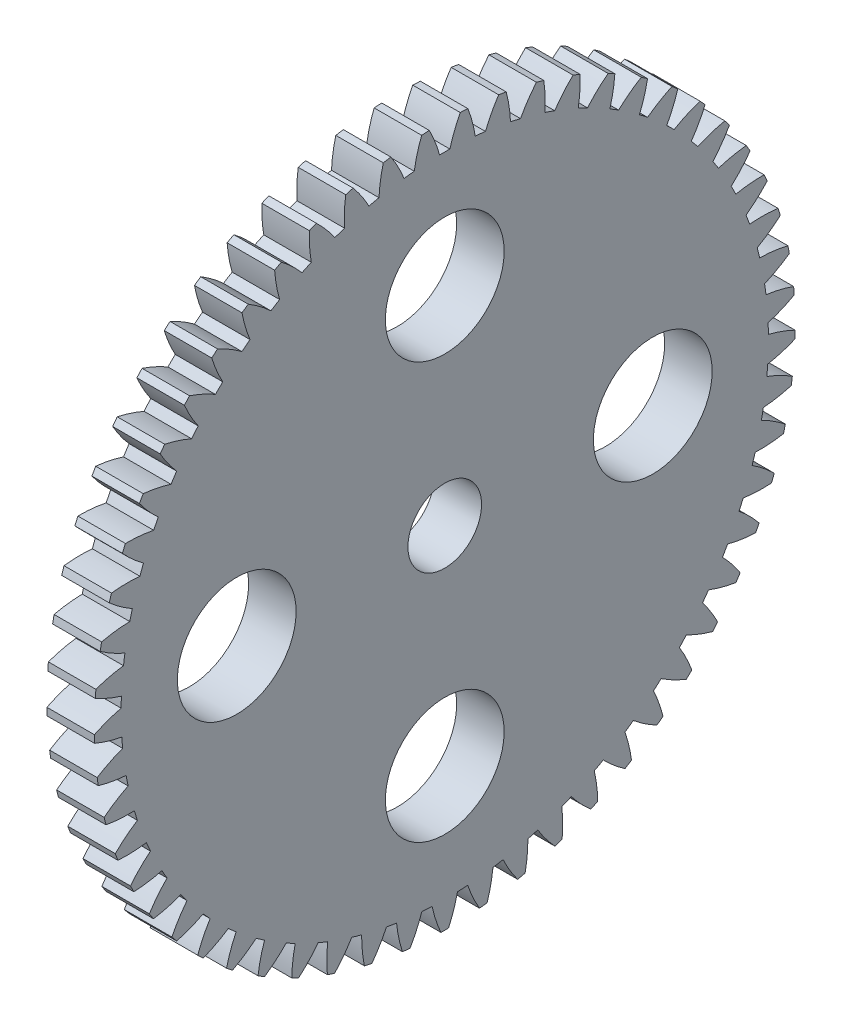
SolidWorks part; units mm, degrees
ref_plane "Plane1" through (0, 0, 0) normal (0, 0, 1) x (1, 0, 0)
ref_plane "Plane2" through (0, 0, 0) normal (0, 1, 0) x (1, 0, 0)
ref_plane "Plane3" through (0, 0, 0) normal (1, 0, 0) x (0, 0, -1)
sketch "HoldingSke" plane through (0, 0, 0) normal (0, 1, 0) x (1, 0, 0)
  line L0 (0, 0) -> (0.5446, -0.8387)
  line L1 (-15, 0) -> (100, 0) construction
  line L2 (0, 0) -> (-2.1039, 2.3779)
  line L3 (0, 0) -> (-11.863, 4.5341)
  line L4 (0, 0) -> (4.7035, 7.2428)
  line L5 (0, 0) -> (-46.8476, -17.4728)
  line L6 (0, 0) -> (-3.3159, -2.2372)
  line L7 (-2.1039, 2.3779) -> (8.6586, 51.2059)
  line L8 (-76.2, 54.61) -> (-75.7, 54.61)
  line L9 (-71.009, 38.7566) -> (-53.1078, 45.2721)
  line L10 (-76.2, 71.12) -> (104.1128, 71.12)
  line L11 (0, 0) -> (-4, 0)
  line L12 (-76.2, 101.6) -> (-76.162, 101.6)
  line L13 (24.9733, 27.94) -> (52.9518, 28.4284)
  line L14 (24.9733, 27.94) -> (24.9743, 27.94)
  line L15 (24.9733, 27.94) -> (100.4006, 29.5858)
  line L16 (-63.627, -1) -> (-12.827, -1)
  circle A0 centre (0, 0) radius 1.5
  circle A1 centre (0, 0) radius 27.249
  circle A2 centre (0, 0) radius 37.5
  circle A3 centre (0, 0) radius 1.5
  dimension "MHD" = 54.498
  dimension "Hub_dia" = 75
  dimension "Bore" = 3
  dimension "MBD" = 3
  dimension "Num_teeth" = 57
  dimension "Pitch" = 1
  dimension "Overall_len" = 50
  dimension "Show_teeth" = 57
  dimension "Thickness" = 4
  dimension "OAL" = 50.0001
  dimension "T_dim" = 0.5
  dimension "Ap" = 20
  dimension "H" = 19.05
  dimension "Pitch_radius" = 180.3128
  dimension "Width" = 4
  dimension "Backlash" = 0.038
  dimension "Addendum_fac" = 1
  dimension "Dedendum_fac" = 1.25
  dimension "Clearance_fac" = 0.25
  dimension "Dedendum_add" = 0.001
  dimension "Module" = 1
sketch "BasProSke" plane through (0, 0, 0) normal (0, 1, 0) x (1, 0, 0)
  line L0 (-10, 0) -> (60, 0) construction
  line L1 (0, 0) -> (0, 29.5)
  line L2 (0, 0) -> (4, 0)
  line L3 (4, 0) -> (4, 29.5)
  line L4 (4, 29.5) -> (0, 29.5)
  dimension "Thickness" = 4
  dimension "Diameter" = 59
revolve "Base-Revolve" add sketch "BasProSke" angle 360 about L0
sketch "TooCutSke" plane through (0, 0, 0) normal (1, 0, 0) x (0, 0, -1)
  line L1 (0, 0) -> (0, 107) construction
  line L2 (0, 0) -> (-0.8518, 28.4873) construction
  line L3 (0, 0) -> (-3.139, 56.8953) construction
  line L4 (-0.8518, 28.4873) -> (-1.5695, 28.4477) construction
  arc A0 (0.4321, 27.2456) -> (-0.4321, 27.2456) centre (0, 0) ccw
  arc A1 (1.3171, 29.496) -> (-1.3171, 29.496) centre (0, 0) ccw
  circle A2 centre (0, 0) radius 28.5 construction
  circle A3 centre (0, 0) radius 26.7812 construction
  arc A4 (-0.4321, 27.2456) -> (-1.3171, 29.496) centre (-11.424, 24.2225) ccw
  arc A5 (1.3171, 29.496) -> (0.4321, 27.2456) centre (11.424, 24.2225) ccw
  dimension "Root_dia" = 54.498
  dimension "Overcut_dia" = 59.0508
  dimension "Pitch_dia" = 57
  dimension "Base_dia" = 53.5625
  dimension "Flank_rad" = 11.4
  dimension "Half_ang" = 3.158
  dimension "Half_CT" = 0.7188
extrude "ToothCut" cut sketch "TooCutSke" along normal through all
fillet "Breaks" [suppressed] radius 0.02
fillet "RootFillets" [suppressed] radius 0.251
pattern_circular "TeethCuts" count 57 every 6.316 about axis through (-10, 0, 0) along (1, 0, 0) of "ToothCut", "RootFillets", "Breaks"
sketch "HubNeaOneSke" plane through (0, 0, 0) normal (-1, 0, 0) x (0, 0, 1)
  circle A0 centre (0, 0) radius 27.249
  dimension "Diameter" = 54.498
extrude "HubNearOne" [suppressed] add sketch "HubNeaOneSke" along normal blind 46.0001
sketch "HubNeaBotSke" plane through (0, 0, 0) normal (-1, 0, 0) x (0, 0, 1)
  circle A0 centre (0, 0) radius 27.249
  dimension "Diameter" = 54.498
extrude "HubNearBoth" [suppressed] add sketch "HubNeaBotSke" along normal blind 23
ref_plane "FarPln" through (4, 0, 0) normal (1, 0, 0) x (0, 0, -1)
sketch "HubFarSke" plane through (4, 0, 0) normal (1, 0, 0) x (0, 0, -1)
  circle A0 centre (0, 0) radius 27.249
  dimension "Diameter" = 54.498
extrude "HubFar" [suppressed] add sketch "HubFarSke" along normal blind 23
sketch "BorSke" plane through (0, 0, 0) normal (1, 0, 0) x (0, 0, -1)
  circle A0 centre (0, 0) radius 3.1
  dimension "Diameter" = 6.2
extrude "Bore" cut sketch "BorSke" along normal mid plane 100.0001
sketch "KeySke" plane through (0, 0, 0) normal (1, 0, 0) x (0, 0, -1)
  line L0 (-0.6, 0) -> (-0.6, 2)
  line L1 (-0.6, 2) -> (0.6, 2)
  line L2 (0.6, 2) -> (0.6, 0)
  line L3 (0, 0) -> (0, 34) construction
  line L4 (-0.6, 0) -> (0.6, 0)
  dimension "Offset" = 2
  dimension "Width" = 1.2
extrude "Keyway" [suppressed] cut sketch "KeySke" along normal mid plane 100.0001
pattern_circular "Keyway2" [suppressed] count 2 every 90 about axis through (-10, 0, 0) along (1, 0, 0)
sketch "Sketch1" plane through (4, 0, 0) normal (1, 0, 0) x (0, 0, -1)
  circle A0 centre (0, -17.5134) radius 5
  circle A1 centre (-17.5134, 0) radius 5
  circle A2 centre (0, 17.5134) radius 5
  circle A3 centre (17.5134, 0) radius 5
  point P11 (0, 0)
  dimension "D2" = 10
  dimension "D1" = 4
extrude "Cut-Extrude1" cut sketch "Sketch1" against normal blind 10
equation "' \"Module@HoldingSke\" = 6.35"
equation "' \"Num_teeth@HoldingSke\" = 12"
equation "' \"Ap@HoldingSke\" =  20"
equation "' \"Ap@HoldingSke\" = 20"
equation "' \"Width@HoldingSke\" = 0.5 * 25.4"
equation "' \"Hub_dia@HoldingSke\"= 1 * 25.4"
equation "' \"Hub_dia@HoldingSke\" = 1 * 25.4"
equation "' \"Overall_len@HoldingSke\" = 1.0 * 25.4"
equation "' \"Bore@HoldingSke\" = 0.75 * 25.4"
equation "' \"T_dim@HoldingSke\" = 0.1 * 25.4"
equation "' \"Width@KeySke\" = 0.25 * 25.4"
equation "' \"Show_teeth@HoldingSke\" = 13"
equation "' \"Backlash@HoldingSke\" = 0.009 * 25.4"
equation "' \"Addendum_fac@HoldingSke\" = 1.0"
equation "' \"Dedendum_fac@HoldingSke\" = 1.25"
equation "' \"Dedendum_add@HoldingSke\" = 0.00005 * 25.4"
equation "' \"Clearance_fac@HoldingSke\" = 0.25"
equation "\"Pitch@HoldingSke\" = 1 / \"Module@HoldingSke\""
equation "\"Overcut_dia@TooCutSke\" = (\"Num_teeth@HoldingSke\" + 2 * \"Addendum_fac@HoldingSke\") / \"Pitch@HoldingSke\" + 0.002 * 25.4"
equation "\"Pitch_dia@TooCutSke\" = \"Num_teeth@HoldingSke\" / \"Pitch@HoldingSke\""
equation "\"Base_dia@TooCutSke\" = \"Num_teeth@HoldingSke\" / \"Pitch@HoldingSke\" * cos((\"Ap@HoldingSke\"  * 3.14159265 / 180))"
equation "\"Root_dia@TooCutSke\" = (\"Num_teeth@HoldingSke\" + 2) / \"Pitch@HoldingSke\" - 2 * (\"Addendum_fac@HoldingSke\" + \"Dedendum_fac@HoldingSke\") / \"Pitch@HoldingSke\" - \"Dedendum_add@HoldingSke\" * 2"
equation "\"Half_ang@TooCutSke\" = 180 / \"Num_teeth@HoldingSke\""
equation "\"Half_CT@TooCutSke\" = \"Num_teeth@HoldingSke\" / \"Pitch@HoldingSke\" * sin((3.14159265 / 2 / \"Num_teeth@HoldingSke\")) / 2 - 7 * \"Backlash@HoldingSke\" / 4"
equation "\"Flank_rad@TooCutSke\" = \"Num_teeth@HoldingSke\" / \"Pitch@HoldingSke\" / 5"
equation "\"Radius@RootFillets\" = \"Clearance_fac@HoldingSke\" / \"Pitch@HoldingSke\" + \"Dedendum_add@HoldingSke\""
equation "\"Break_rad@Breaks\" = 0.02 / \"Pitch@HoldingSke\""
equation "\"Thickness@HoldingSke\" = \"Width@HoldingSke\""
equation "\"OAL@HoldingSke\" = \"Thickness@HoldingSke\""
equation "\"MHD@HoldingSke\" = (\"Num_teeth@HoldingSke\" + 2) / \"Pitch@HoldingSke\" - 2 * (\"Addendum_fac@HoldingSke\" + \"Dedendum_fac@HoldingSke\")  / \"Pitch@HoldingSke\" - \"Dedendum_add@HoldingSke\" * 2"
equation "\"MBD@HoldingSke\" = (\"Num_teeth@HoldingSke\" + 2) / \"Pitch@HoldingSke\" - 2 * (\"Addendum_fac@HoldingSke\" + \"Dedendum_fac@HoldingSke\")  / \"Pitch@HoldingSke\" - \"Dedendum_add@HoldingSke\" * 2 - 0.002 * 25.4"
equation "\"MHD@HoldingSke\" = ((sgn( \"MHD@HoldingSke\" - \"Hub_dia@HoldingSke\" )-1)*( \"MHD@HoldingSke\" - \"Hub_dia@HoldingSke\" ))/-2+ \"Hub_dia@HoldingSke\""
equation "\"MBD@HoldingSke\" = ((sgn( \"MBD@HoldingSke\" - \"Bore@HoldingSke\" )-1)*( \"MBD@HoldingSke\" - \"Bore@HoldingSke\" ))/-2+ \"Bore@HoldingSke\""
equation "\"OAL@HoldingSke\" = ((sgn( \"OAL@HoldingSke\" - \"Overall_len@HoldingSke\" )+1)*( \"OAL@HoldingSke\" - \"Overall_len@HoldingSke\" ))/2 + \"Overall_len@HoldingSke\" + 0.000002 * 25.4"
equation "\"Num_teeth@TeethCuts\" = int( \"Show_teeth@HoldingSke\" ) + 1"
equation "\"Num_teeth@TeethCuts\" = ((sgn( \"Num_teeth@TeethCuts\" - \"Num_teeth@HoldingSke\" )-1)*( \"Num_teeth@TeethCuts\" - \"Num_teeth@HoldingSke\" ))/-2+ \"Num_teeth@HoldingSke\""
equation "\"Num_teeth@TeethCuts\" = ((sgn( \"Num_teeth@TeethCuts\" - 2.0)+1)*( \"Num_teeth@TeethCuts\" - 2.0))/2 +2.0"
equation "\"Angle@TeethCuts\" = 360.0 / \"Num_teeth@HoldingSke\""
equation "\"Diameter@BasProSke\" = (\"Num_teeth@HoldingSke\" + 2 * \"Addendum_fac@HoldingSke\") / \"Pitch@HoldingSke\""
equation "\"Thickness@BasProSke\"  = \"Thickness@HoldingSke\""
equation "' \"Fillet_rad@BasProSke\" =  \"Thickness@HoldingSke\" * 0.05"
equation "' \"Fillet_rad@BasProSke\" = \"Thickness@HoldingSke\" * 0.05"
equation "\"MHD@HoldingSke\" = ((sgn( \"MHD@HoldingSke\" - \"Root_dia@TooCutSke\" )-1)*( \"MHD@HoldingSke\" - \"Root_dia@TooCutSke\" ))/-2+ \"Root_dia@TooCutSke\""
equation "\"Diameter@HubNeaOneSke\" = \"MHD@HoldingSke\""
equation "\"Length@HubNearOne\" = \"OAL@HoldingSke\" - \"Thickness@BasProSke\""
equation "\"Diameter@HubNeaBotSke\" = \"MHD@HoldingSke\""
equation "\"Length@HubNearBoth\" = ( \"OAL@HoldingSke\" - \"Thickness@BasProSke\" ) / 2.0"
equation "\"Thickness@FarPln\" = \"Thickness@BasProSke\""
equation "\"Diameter@HubFarSke\" = \"MHD@HoldingSke\""
equation "\"Length@HubFar\" = ( \"OAL@HoldingSke\" - \"Thickness@BasProSke\" ) / 2.0"
equation "\"D1@Bore\" = \"OAL@HoldingSke\" * 2.0"
equation "\"D1@Keyway\" = \"OAL@HoldingSke\" * 2.0"
equation "\"Offset@KeySke\" = \"T_dim@HoldingSke\" + \"MBD@HoldingSke\" / 2.0"
